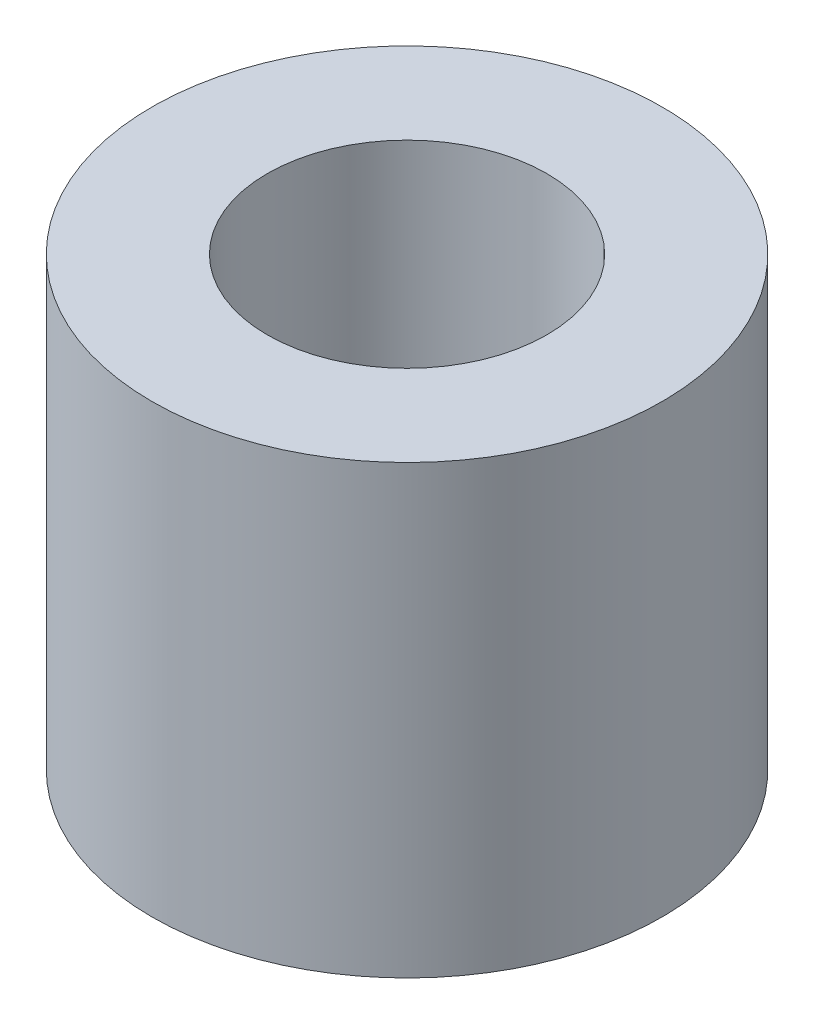
SolidWorks part; units mm, degrees
material "NEOPRENE"
ref_plane "Front Plane" through (0, 0, 0) normal (0, 0, 1) x (1, 0, 0)
ref_plane "Top Plane" through (0, 0, 0) normal (0, 1, 0) x (1, 0, 0)
ref_plane "Right Plane" through (0, 0, 0) normal (1, 0, 0) x (0, 0, -1)
sketch "Sketch1" plane through (0, 0, 0) normal (0, 1, 0) x (1, 0, 0)
  circle A0 centre (0, 0) radius 4
  circle A1 centre (0, 0) radius 2.1914
  dimension "D1" = 8
extrude "Boss-Extrude1" add sketch "Sketch1" along normal blind 7
